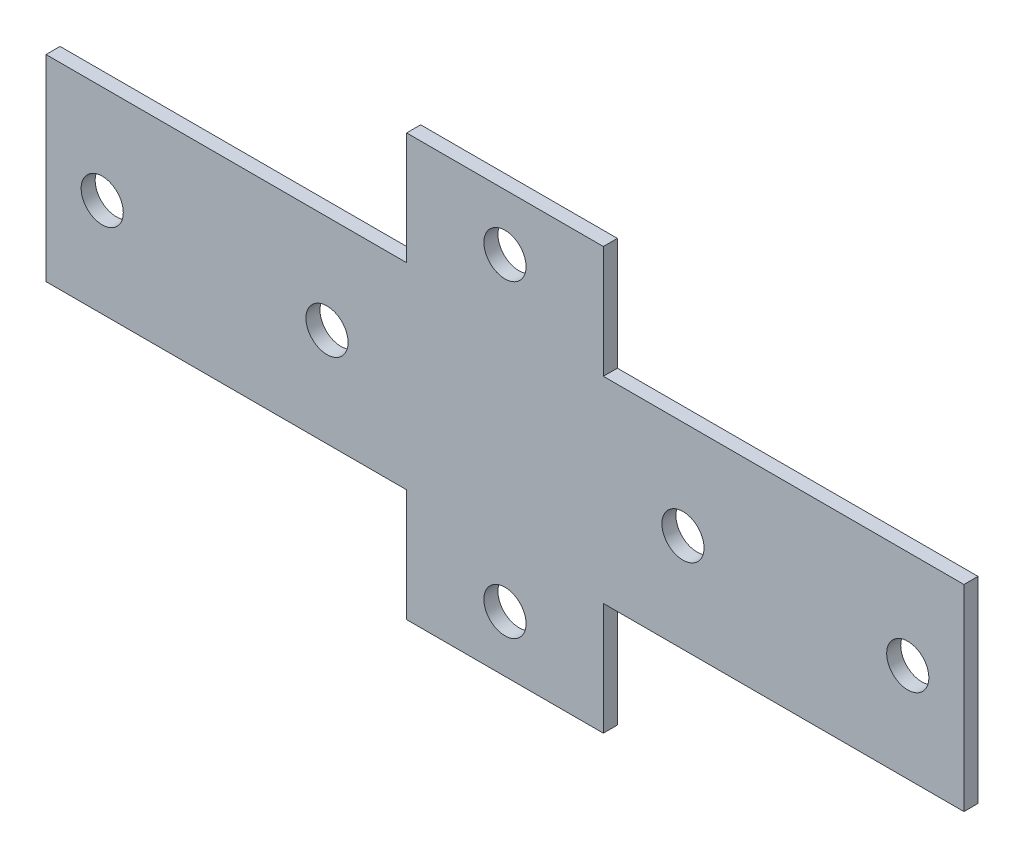
SolidWorks part; units mm, degrees
ref_plane "Спереди" through (0, 0, 0) normal (0, 0, 1) x (1, 0, 0)
ref_plane "Сверху" through (0, 0, 0) normal (0, 1, 0) x (1, 0, 0)
ref_plane "Справа" through (0, 0, 0) normal (1, 0, 0) x (0, 0, -1)
sketch "Эскиз1" plane through (0, 0, 0) normal (0, 0, 1) x (1, 0, 0)
  line L0 (21, -21) -> (98, -21)
  line L1 (-98, 21) -> (-21, 21)
  line L2 (-98, 21) -> (-98, -21)
  line L3 (-98, -21) -> (-21, -21)
  line L4 (98, 21) -> (98, -21)
  line L5 (-98, 21) -> (98, -21) construction
  line L6 (-98, -21) -> (98, 21) construction
  line L7 (-21, -45) -> (21, -45)
  line L8 (-21, -45) -> (-21, -21)
  line L9 (-21, 45) -> (21, 45)
  line L10 (21, -45) -> (21, -21)
  line L11 (-21, -45) -> (21, 45) construction
  line L12 (-21, 45) -> (21, -45) construction
  line L13 (21, 21) -> (98, 21)
  line L14 (-21, 21) -> (-21, 45)
  line L15 (21, 21) -> (21, 45)
  line L16 (0, 33) -> (0, -33) construction
  line L17 (0, 33) -> (0, 45) construction
  line L18 (-86, 0) -> (-98, 0) construction
  circle A0 centre (0, 33) radius 4.5
  circle A1 centre (0, -33) radius 4.5
  circle A2 centre (-86, 0) radius 4.5
  circle A3 centre (-38, 0) radius 4.5
  circle A4 centre (38, 0) radius 4.5
  circle A5 centre (86, 0) radius 4.5
  point P0 (0, 0)
  point P6 (0, 0)
  dimension "D4" = 12
  dimension "D5" = 9
  dimension "D6" = 48
  dimension "D1" = 196
  dimension "D2" = 90
  dimension "D3" = 42
extrude "Бобышка-Вытянуть1" add sketch "Эскиз1" along normal blind 3
